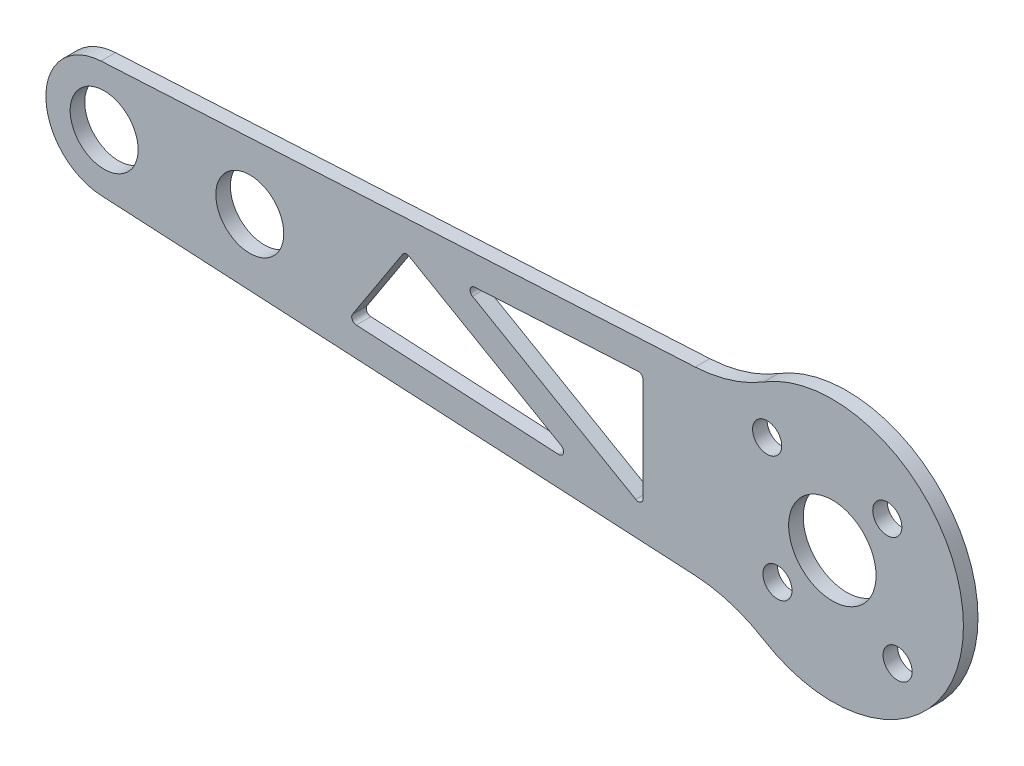
SolidWorks part; units mm, degrees
ref_plane "前视基准面" through (0, 0, 0) normal (0, 0, 1) x (1, 0, 0)
ref_plane "上视基准面" through (0, 0, 0) normal (0, 1, 0) x (1, 0, 0)
ref_plane "右视基准面" through (0, 0, 0) normal (1, 0, 0) x (0, 0, -1)
sketch "草图1" plane through (0, 0, 0) normal (0, 0, 1) x (1, 0, 0)
  line L0 (-104.9237, 0) -> (42.8999, 0) construction
  line L1 (0, 29.5835) -> (0, -29.1295) construction
  line L2 (-20.8265, -20.8265) -> (25.6666, 25.6666) construction
  line L3 (-39.0338, 39.0338) -> (25.5988, -25.5988) construction
  line L4 (-14.1198, 9.2988) -> (-75.3238, 5.9913)
  line L5 (-14.1198, -9.2988) -> (-75.3238, -5.9913)
  line L6 (-19.5, 5.4759) -> (-19.5, -5.1376)
  line L7 (-20.25, -5.5706) -> (-37.0597, 4.1345)
  line L8 (-36.8367, 5.0668) -> (-20.027, 5.9752)
  line L9 (-43.5934, 4.4426) -> (-27.9297, -4.6008)
  line L10 (-28.2067, -5.5331) -> (-49.0308, -4.4078)
  line L11 (-49.4227, -3.6355) -> (-44.2623, 4.2826)
  arc A0 (-7.0717, -11.4996) -> (-7.0717, 11.4996) centre (0, 0) ccw
  circle A5 centre (-5.6569, -5.6569) radius 1.5
  circle A6 centre (-6.7175, 6.7175) radius 1.5
  circle A7 centre (5.6569, 5.6569) radius 1.5
  circle A8 centre (6.7175, -6.7175) radius 1.5
  circle A9 centre (0, 0) radius 4.5
  circle A10 centre (-60, 0) radius 3.5
  circle A11 centre (-75, 0) radius 3.5
  arc A12 (-75.3238, 5.9913) -> (-75.3238, -5.9913) centre (-75, 0) ccw
  arc A13 (-14.1198, -9.2988) -> (-7.0717, -11.4996) centre (-14.9292, -24.2769) cw
  arc A14 (-14.1198, 9.2988) -> (-7.0717, 11.4996) centre (-14.9292, 24.2769) ccw
  arc A18 (-43.5934, 4.4426) -> (-44.2623, 4.2826) centre (-43.8434, 4.0096) ccw
  arc A19 (-49.4227, -3.6355) -> (-49.0308, -4.4078) centre (-49.0038, -3.9085) ccw
  arc A20 (-28.2067, -5.5331) -> (-27.9297, -4.6008) centre (-28.1797, -5.0339) ccw
  arc A21 (-37.0597, 4.1345) -> (-36.8367, 5.0668) centre (-36.8097, 4.5675) cw
  arc A22 (-20.027, 5.9752) -> (-19.5, 5.4759) centre (-20, 5.4759) cw
  arc A23 (-20.25, -5.5706) -> (-19.5, -5.1376) centre (-20, -5.1376) ccw
  point P26 (-13.5, 0)
  point P30 (-19.5, -6.0036)
  point P33 (0, 0)
  point P36 (-9.5459, -9.5459)
  point P39 (-9.5459, 9.5459)
  point P40 (-19.5, -6.0036)
  point P44 (-19.5, 6.0343)
  point P49 (-54.7307, -4.0997)
  point P54 (-44.0036, 4.6794)
  point P65 (-19.5, -6.0036)
  dimension "D1" = 27
  dimension "D2" = 15
  dimension "D3" = 3
  dimension "D4" = 3
  dimension "D7" = 9
  dimension "D8" = 7
  dimension "D9" = 7
  dimension "D11" = 12
  dimension "D5" = 19
  dimension "D6" = 16
  dimension "D10" = 15
  dimension "D12" = 60
  dimension "D13" = 3
  dimension "D14" = 3
  dimension "D15" = 60
  dimension "D18" = 3
  dimension "D19" = 6
  dimension "D20" = 60
extrude "凸台-拉伸1" add sketch "草图1" along normal blind 1.5
